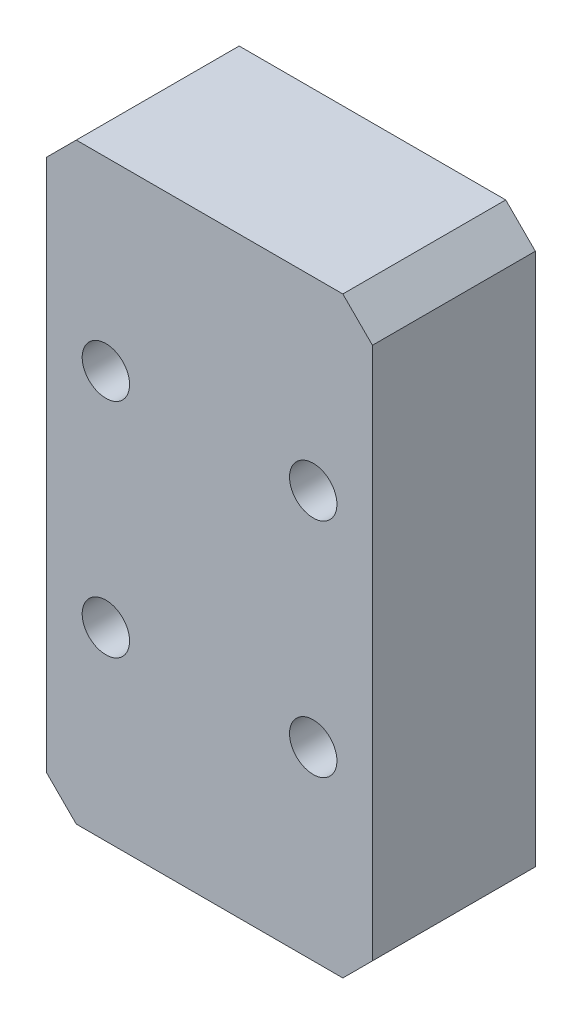
SolidWorks part; units mm, degrees
material "鑄碳鋼"
ref_plane "前基準面" through (0, 0, 0) normal (0, 0, 1) x (1, 0, 0)
ref_plane "上基準面" through (0, 0, 0) normal (0, 1, 0) x (1, 0, 0)
ref_plane "右基準面" through (0, 0, 0) normal (1, 0, 0) x (0, 0, -1)
sketch "草圖1" plane through (0, 0, 0) normal (0, 0, 1) x (1, 0, 0)
  line L1 (-11, -20) -> (11, -20)
  line L2 (-11, -20) -> (-11, 20)
  line L3 (-11, 20) -> (11, 20)
  line L4 (11, -20) -> (11, 20)
  line L5 (-11, -20) -> (11, 20) construction
  line L6 (-11, 20) -> (11, -20) construction
  point P0 (0, 0)
  dimension "D1" = 22
  dimension "D2" = 40
extrude "填料-伸長1" add sketch "草圖1" along normal blind 11
sketch "草圖4" plane through (0, 0, 11) normal (0, 0, 1) x (1, 0, 0)
  line L0 (0, 0) -> (-7, 0) construction
  line L1 (-7, 0) -> (-7, 7.5) construction
  circle A0 centre (-7, 7.5) radius 1.6
  dimension "D3" = 3.2
  dimension "D1" = 7
  dimension "D2" = 7.5
extrude "除料-伸長3" cut sketch "草圖4" against normal through all
pattern_linear "直線複製排列1" count 2 spacing 14 along (1, 0, 0) count 2 spacing 15 along (0, -1, 0) of "除料-伸長3"
chamfer "導角1" distance 2 angle 45 4 edges at (11, -20, 5.5) (-11, -20, 5.5) (-11, 20, 5.5) (11, 20, 5.5)
